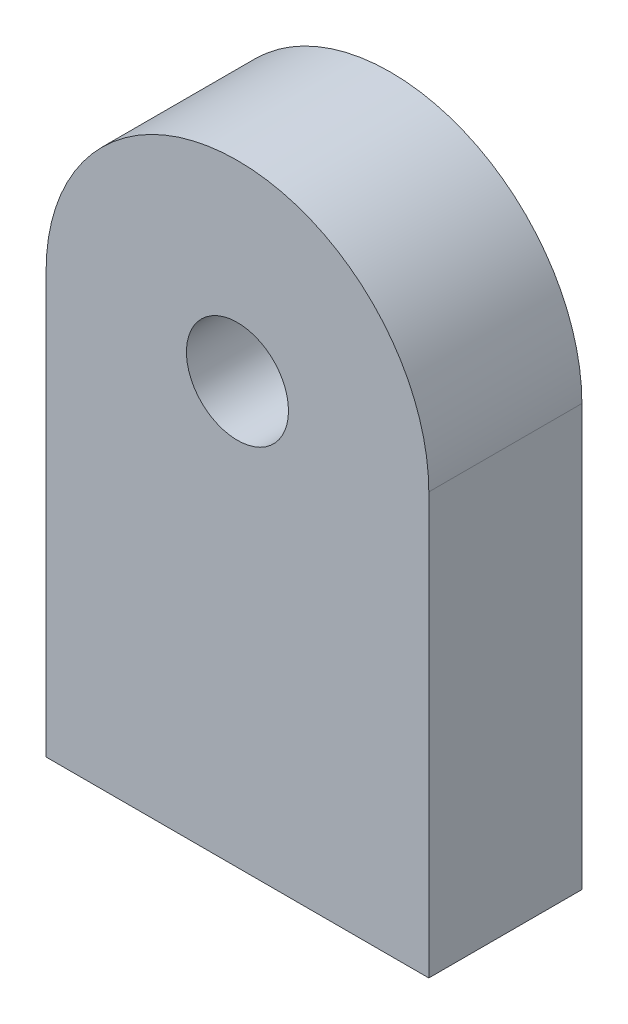
SolidWorks part; units mm, degrees
ref_plane "Front Plane" through (0, 0, 0) normal (0, 0, 1) x (1, 0, 0)
ref_plane "Top Plane" through (0, 0, 0) normal (0, 1, 0) x (1, 0, 0)
ref_plane "Right Plane" through (0, 0, 0) normal (1, 0, 0) x (0, 0, -1)
sketch "Sketch2" plane through (0, 0, 0) normal (0, 0, 1) x (1, 0, 0)
  circle A0 centre (0, 0) radius 15
  circle A1 centre (0, 0) radius 11
  dimension "D1" = 30
  dimension "D2" = 22
extrude "Boss-Extrude1" add sketch "Sketch2" along normal blind 4
sketch "Sketch3" plane through (0, 0, 4) normal (0, 0, 1) x (1, 0, 0)
  circle A0 centre (0, 0) radius 15
  circle A1 centre (0, 0) radius 4
  circle A2 centre (0, 0) radius 15 construction
  dimension "D1" = 8
  dimension "D2" = 0
extrude "Boss-Extrude2" add sketch "Sketch3" along normal blind 8
sketch "Sketch6" plane through (0, 0, 12) normal (0, 0, 1) x (1, 0, 0)
  line L0 (-15, 0) -> (-15, -33)
  line L1 (15, 0) -> (15, -33)
  line L2 (15, -33) -> (-15, -33)
  circle A0 centre (0, 0) radius 15 construction
  circle A2 centre (0, 0) radius 15
  arc A3 (-15, 0) -> (15, 0) centre (0, 0) ccw
  dimension "D1" = 33
  dimension "D2" = 0
extrude "Boss-Extrude5" add sketch "Sketch6" against normal blind 12
sketch "Sketch7" plane through (0, -33, 0) normal (0, -1, 0) x (1, 0, 0)
  line L0 (15, 0) -> (15, 12) construction
  line L1 (-15, 0) -> (-15, 12) construction
  line L2 (-15, 12) -> (15, 12) construction
  circle A0 centre (7, 6) radius 3
  circle A1 centre (-7, 6) radius 3
  dimension "D1" = 6
  dimension "D4" = 6
  dimension "D2" = 8
  dimension "D3" = 8
  dimension "D5" = 6
  dimension "D6" = 6
extrude "Cut-Extrude1" cut sketch "Sketch7" against normal blind 14
